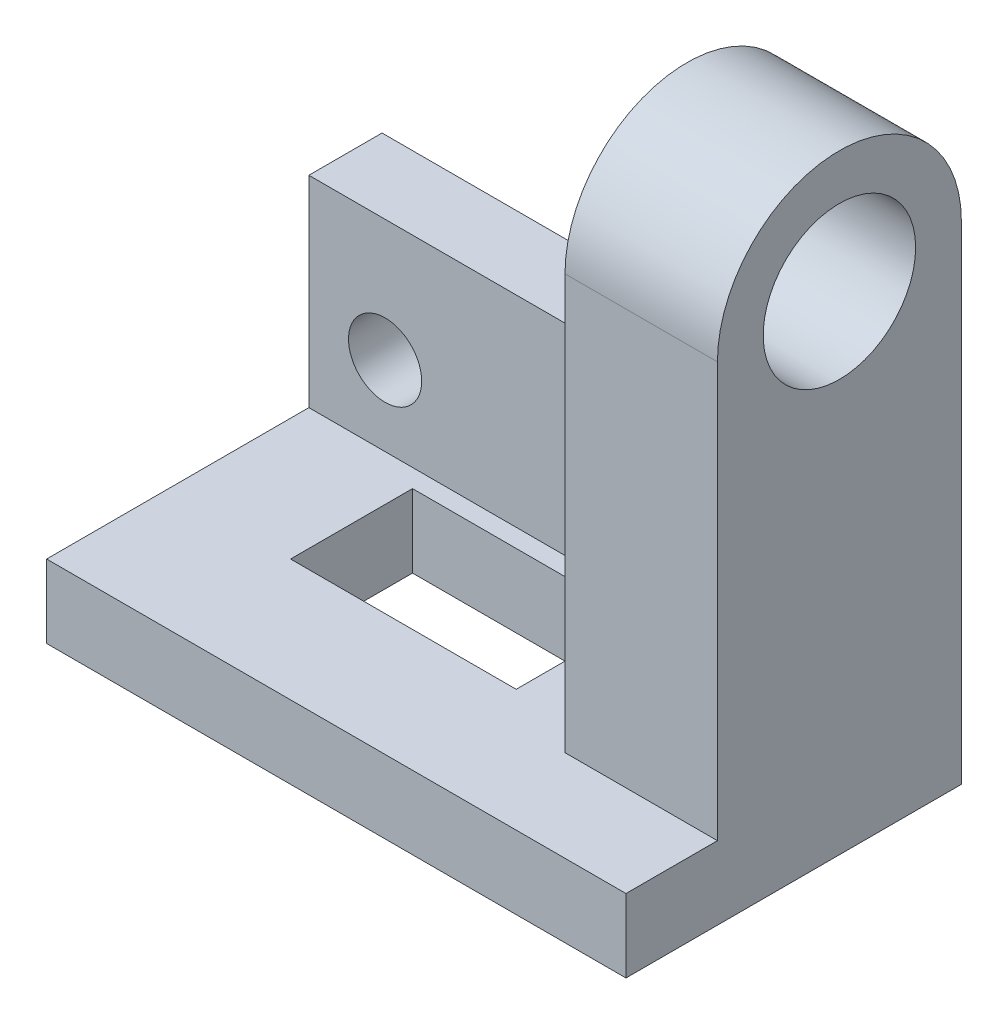
SolidWorks part; units mm, degrees
ref_plane "Front Plane" through (0, 0, 0) normal (0, 0, 1) x (1, 0, 0)
ref_plane "Top Plane" through (0, 0, 0) normal (0, 1, 0) x (1, 0, 0)
ref_plane "Right Plane" through (0, 0, 0) normal (1, 0, 0) x (0, 0, -1)
sketch "Sketch1" plane through (0, 0, 0) normal (0, 0, 1) x (1, 0, 0)
  line L1 (-37.5143, 7.3609) -> (57.4857, 7.3609)
  line L2 (-37.5143, 7.3609) -> (-37.5143, -25.6391)
  line L3 (-37.5143, -25.6391) -> (57.4857, -25.6391)
  line L4 (57.4857, 7.3609) -> (57.4857, -25.6391)
  dimension "D1" = 33
  dimension "D2" = 95
  dimension "D3" = 57.4857
  dimension "D4" = 7.3609
extrude "Boss-Extrude1" add sketch "Sketch1" against normal blind 12
sketch "Sketch2" plane through (0, 0, 0) normal (0, 0, 1) x (1, 0, 0)
  line L0 (-37.5143, 7.3609) -> (-37.5143, -25.6391) construction
  line L1 (-37.5143, -25.6391) -> (57.4857, -25.6391) construction
  circle A0 centre (-25.0143, -12.6391) radius 6
  circle A1 centre (16.4857, -12.6391) radius 6
  dimension "D1" = 12
  dimension "D2" = 12.5
  dimension "D3" = 54
  dimension "D4" = 13
extrude "Cut-Extrude1" cut sketch "Sketch2" against normal blind 12
sketch "Sketch3" plane through (0, 0, 0) normal (0, 0, 1) x (1, 0, 0)
  line L0 (32.4857, 42.3609) -> (32.4857, -25.6391)
  line L1 (-37.5143, 7.3609) -> (-37.5143, -25.6391) construction
  line L3 (-37.5143, -25.6391) -> (57.4857, -25.6391) construction
  line L6 (57.4857, 42.3609) -> (32.4857, 42.3609)
  line L9 (57.4857, 42.3609) -> (57.4857, -25.6391)
  line L10 (57.4857, -25.6391) -> (32.4857, -25.6391)
  dimension "D1" = 68
  dimension "D2" = 70
extrude "Boss-Extrude2" add sketch "Sketch3" along normal blind 28 and the other way blind 12
sketch "Sketch4" plane through (57.4857, 0, 0) normal (1, 0, 0) x (0, 0, -1)
  line L0 (12, 42.3609) -> (-28, 42.3609) construction
  circle A0 centre (-8, 42.3609) radius 20
  dimension "D1" = 40
extrude "Boss-Extrude3" add sketch "Sketch4" against normal blind 25
sketch "Sketch5" plane through (57.4857, 0, 0) normal (1, 0, 0) x (0, 0, -1)
  circle A0 centre (-8, 42.3609) radius 12.5
  dimension "D1" = 25
extrude "Cut-Extrude2" cut sketch "Sketch5" against normal blind 25
sketch "Sketch6" plane through (0, -25.6391, 0) normal (0, -1, 0) x (1, 0, 0)
  line L0 (57.4857, -12) -> (57.4857, 28) construction
  line L1 (57.4857, 43) -> (-37.5143, 43)
  line L2 (-37.5143, 43) -> (-37.5143, -12)
  line L3 (-37.5143, -12) -> (57.4857, -12)
  line L4 (57.4857, -12) -> (57.4857, 43)
  line L5 (-37.5143, -12) -> (57.4857, -12) construction
  dimension "D1" = 55
extrude "Boss-Extrude4" add sketch "Sketch6" along normal blind 12
sketch "Sketch7" plane through (0, -25.6391, 0) normal (0, 1, 0) x (1, 0, 0)
  line L0 (32.4857, 0) -> (32.4857, -28) construction
  line L1 (-37.5143, 0) -> (32.4857, 0) construction
  line L4 (-17.5143, -23) -> (19.4857, -23)
  line L5 (-17.5143, -23) -> (-17.5143, -3)
  line L6 (-17.5143, -3) -> (19.4857, -3)
  line L7 (19.4857, -23) -> (19.4857, -3)
  dimension "D1" = 20
  dimension "D2" = 37
  dimension "D3" = 13
  dimension "D4" = 3
extrude "Cut-Extrude3" cut sketch "Sketch7" against normal blind 12
fillet "Fillet1" radius 8 1 edges at (32.4857, 7.3609, -6)
ref_plane "Plane2" through (32.4857, 7.3609, -12) normal (-1, 0, 0) x (0, 0, 1)
